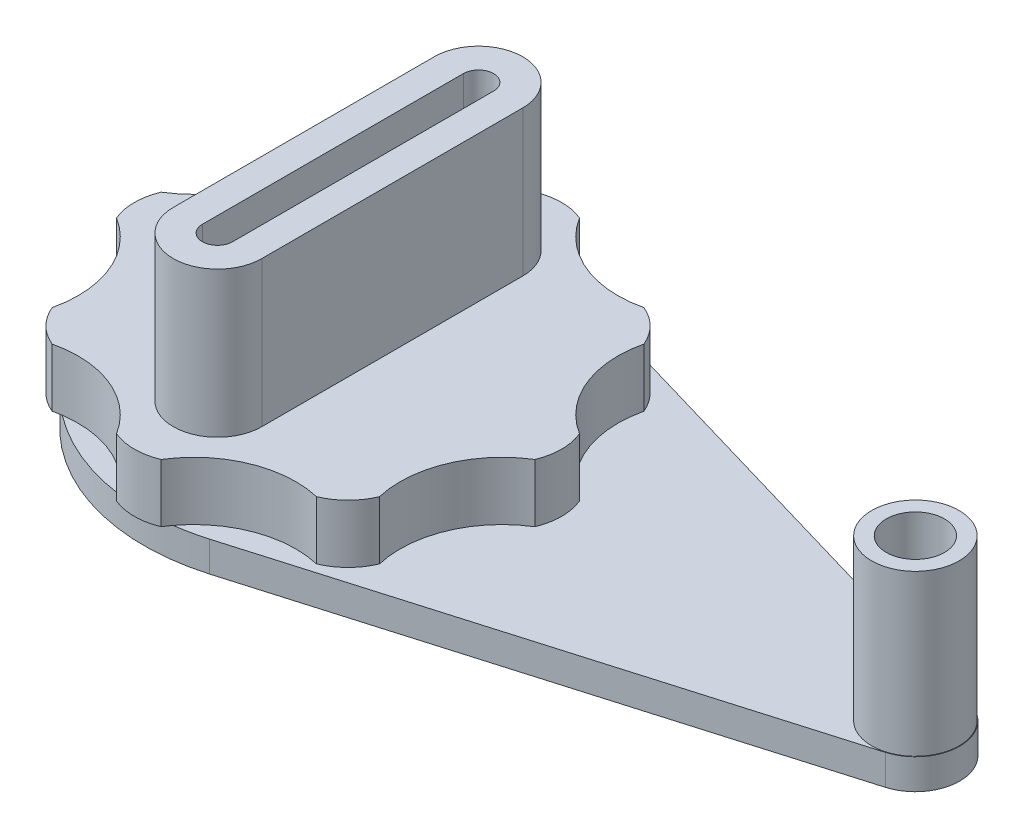
SolidWorks part; units mm, degrees
ref_plane "Front Plane" through (0, 0, 0) normal (0, 0, 1) x (1, 0, 0)
ref_plane "Top Plane" through (0, 0, 0) normal (0, 1, 0) x (1, 0, 0)
ref_plane "Right Plane" through (0, 0, 0) normal (1, 0, 0) x (0, 0, -1)
sketch "Sketch1" plane through (0, 0, 0) normal (0, 1, 0) x (1, 0, 0)
  line L0 (6.2522, 21.3275) -> (63.2066, 4.6311)
  line L1 (6.2522, -21.3275) -> (63.2066, -4.6311)
  line L2 (0, 0) -> (61.849, 0) construction
  arc A0 (6.2522, 21.3275) -> (6.2522, -21.3275) centre (0, 0) ccw
  arc A1 (63.2066, -4.6311) -> (63.2066, 4.6311) centre (61.849, 0) ccw
  dimension "D1" = 44.45
  dimension "D2" = 9.652
  dimension "D3" = 88.9
extrude "Boss-Extrude1" add sketch "Sketch1" along normal mid plane 3.302
sketch "Sketch2" plane through (0, 1.651, 0) normal (0, 1, 0) x (1, 0, 0)
  line L0 (17.8445, -14.4079) -> (22.8059, -2.43) construction
  line L1 (14.4079, 17.8445) -> (2.43, 22.8059) construction
  line L2 (-2.43, 22.8059) -> (-14.4079, 17.8445) construction
  line L3 (-17.8445, 14.4079) -> (-22.8059, 2.43) construction
  line L4 (-22.8059, -2.43) -> (-17.8445, -14.4079) construction
  line L5 (-14.4079, -17.8445) -> (-2.43, -22.8059) construction
  line L6 (2.43, -22.8059) -> (14.4079, -17.8445) construction
  line L7 (22.8059, 2.43) -> (17.8445, 14.4079) construction
  line L8 (-23.8125, 0) -> (23.8125, 0) construction
  arc A0 (-17.8445, 14.4079) -> (-14.4079, 17.8445) centre (-11.9779, 11.9779) cw
  arc A2 (-22.8059, -2.43) -> (-22.8059, 2.43) centre (-16.9393, 0) cw
  arc A3 (-17.8445, -14.4079) -> (-14.4079, -17.8445) centre (-11.9779, -11.9779) ccw
  arc A4 (-2.43, -22.8059) -> (2.43, -22.8059) centre (0, -16.9393) ccw
  arc A5 (14.4079, -17.8445) -> (17.8445, -14.4079) centre (11.9779, -11.9779) ccw
  arc A6 (22.8059, 2.43) -> (22.8059, -2.43) centre (16.9393, 0) cw
  arc A7 (14.4079, 17.8445) -> (17.8445, 14.4079) centre (11.9779, 11.9779) cw
  arc A8 (2.43, 22.8059) -> (-2.43, 22.8059) centre (0, 16.9393) ccw
  arc A9 (-14.4079, 17.8445) -> (-2.43, 22.8059) centre (-11.873, 28.6641) ccw
  arc A10 (2.43, 22.8059) -> (14.4079, 17.8445) centre (11.873, 28.6641) ccw
  arc A11 (17.8445, 14.4079) -> (22.8059, 2.43) centre (28.6641, 11.873) ccw
  arc A12 (22.8059, -2.43) -> (17.8445, -14.4079) centre (28.6641, -11.873) ccw
  arc A13 (14.4079, -17.8445) -> (2.43, -22.8059) centre (11.873, -28.6641) ccw
  arc A14 (-2.43, -22.8059) -> (-14.4079, -17.8445) centre (-11.873, -28.6641) ccw
  arc A15 (-17.8445, -14.4079) -> (-22.8059, -2.43) centre (-28.6641, -11.873) ccw
  arc A16 (-22.8059, 2.43) -> (-17.8445, 14.4079) centre (-28.6641, 11.873) ccw
  point P14 (0, 0)
  point P52 (0, 0)
  dimension "D2" = 6.35
  dimension "D3" = 11.1125
  dimension "D1" = 47.625
  dimension "D4" = 8
extrude "Boss-Extrude2" add sketch "Sketch2" along normal blind 6.35
sketch "Sketch4" plane through (0, 8.001, 0) normal (0, 1, 0) x (1, 0, 0)
  line L0 (0, -14.224) -> (0, 14.224) construction
  line L1 (-4.826, -14.224) -> (-4.826, 14.224)
  line L2 (4.826, -14.224) -> (4.826, 14.224)
  line L3 (-1.651, -14.224) -> (-1.651, 14.224)
  line L4 (1.651, -14.224) -> (1.651, 14.224)
  arc A0 (-4.826, -14.224) -> (4.826, -14.224) centre (0, -14.224) ccw
  arc A1 (4.826, 14.224) -> (-4.826, 14.224) centre (0, 14.224) ccw
  arc A3 (1.651, 14.224) -> (-1.651, 14.224) centre (0, 14.224) ccw
  arc A4 (-1.651, -14.224) -> (1.651, -14.224) centre (0, -14.224) ccw
  point P2 (0, 0)
  point P21 (0, 19.05)
  dimension "D1" = 9.652
  dimension "D3" = 38.1
  dimension "D2" = 3.175
extrude "Boss-Extrude3" add sketch "Sketch4" along normal blind 22.225 from surface at -6.35 starting at face at (21.2094, 1.651, 0)
sketch "Sketch5" plane through (0, 1.651, 0) normal (0, 1, 0) x (1, 0, 0)
  circle A0 centre (61.849, 0) radius 4.7625
  arc A6 (63.2066, -4.6311) -> (63.2066, 4.6311) centre (61.849, 0) ccw construction
  dimension "D1" = 9.525
  dimension "D3" = 61.849
extrude "Boss-Extrude4" add sketch "Sketch5" along normal blind 19.05 from offset 1.5875 offset against normal yes
sketch "Sketch6" plane through (0, 19.1135, 0) normal (0, 1, 0) x (1, 0, 0)
  circle A0 centre (61.849, 0) radius 3.175
  circle A1 centre (61.849, 0) radius 4.7625 construction
  dimension "D1" = 6.35
extrude "Cut-Extrude1" cut sketch "Sketch6" against normal up to surface (17.4625 mm away) up to face at (61.849, 1.651, 4.7625)
ref_plane "BOTTOM PLANE" through (0, -1.651, 0) normal (0, -1, 0) x (-1, 0, 0)
sketch "Sketch7" plane through (0, -1.651, 0) normal (0, 1, 0) x (1, 0, 0)
  circle A0 centre (0, 0) radius 19.05
  dimension "D1" = 38.1
extrude "Cut-Extrude3" cut sketch "Sketch7" along normal blind 6.35
sketch "Sketch8" plane through (0, 4.699, 0) normal (0, -1, 0) x (1, 0, 0)
  circle A0 centre (0, 0) radius 13.335
  circle A1 centre (0, 0) radius 9.525
  dimension "D1" = 26.67
  dimension "D2" = 19.05
extrude "Boss-Extrude5" add sketch "Sketch8" along normal blind 7.9375
sketch "Sketch9" plane through (0, 4.699, 0) normal (0, -1, 0) x (1, 0, 0)
  circle A0 centre (0, 0) radius 4.7625
  dimension "D1" = 9.525
extrude "Boss-Extrude6" add sketch "Sketch9" along normal blind 12.7
fillet "Fillet3" radius 3.81 1 edges at (0, -8.001, -4.7625)
